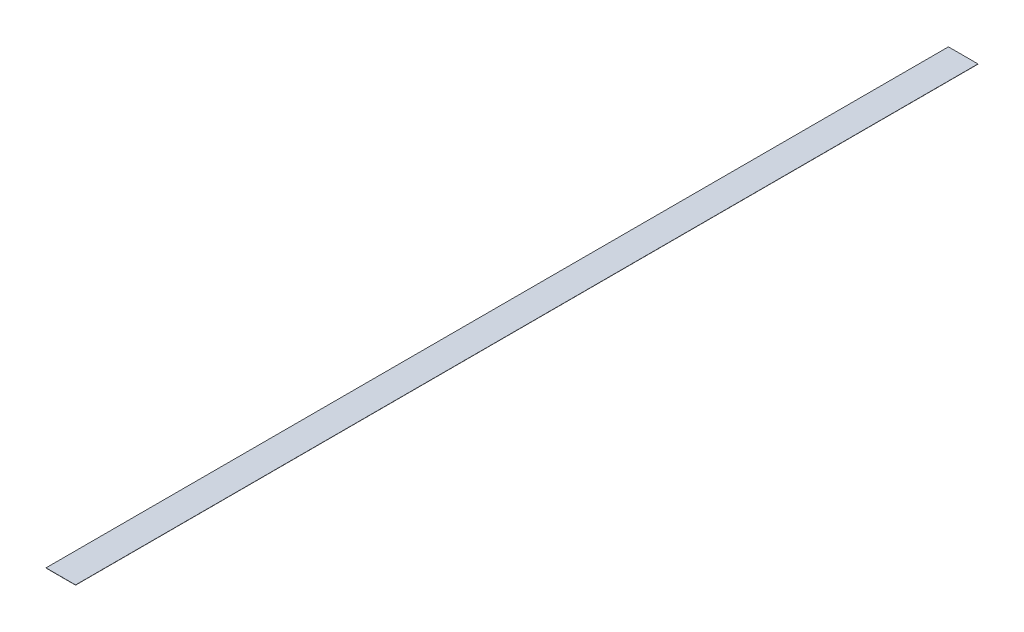
SolidWorks part; units mm, degrees
material "Kapton Film"
ref_plane "Front Plane" through (0, 0, 0) normal (0, 0, 1) x (1, 0, 0)
ref_plane "Top Plane" through (0, 0, 0) normal (0, 1, 0) x (1, 0, 0)
ref_plane "Right Plane" through (0, 0, 0) normal (1, 0, 0) x (0, 0, -1)
sketch "Sketch1" plane through (0, 0, 0) normal (0, 1, 0) x (1, 0, 0)
  line L5 (0, 0) -> (15, 0)
  line L6 (0, 0) -> (0, -457.6)
  line L7 (0, -457.6) -> (15, -457.6)
  line L8 (15, 0) -> (15, -457.6)
  dimension "D1" = 457.6
  dimension "D2" = 15
extrude "Boss-Extrude1" add sketch "Sketch1" along normal blind 0.1 contours L6 L7 L8 L5
sketch "Sketch2" plane through (0, 0.1, 0) normal (0, 1, 0) x (1, 0, 0)
  line L0 (0, -437.6) -> (15, -434.137) construction
  line L1 (0, 0) -> (0, -457.6) construction
  line L2 (15, 0) -> (15, -457.6) construction
  line L3 (5.0641, -436.4309) -> (5.0641, -407.8309) construction
  circle A0 centre (5.0641, -436.4309) radius 1
  circle A1 centre (9.9359, -435.3061) radius 1
  circle A2 centre (5.0641, -407.8309) radius 1
  circle A3 centre (9.9359, -406.7061) radius 1
  circle A4 centre (5.0641, -379.2309) radius 1
  circle A5 centre (9.9359, -378.1061) radius 1
  circle A6 centre (5.0641, -350.6309) radius 1
  circle A7 centre (9.9359, -349.5061) radius 1
  circle A8 centre (5.0641, -322.0309) radius 1
  circle A9 centre (9.9359, -320.9061) radius 1
  circle A10 centre (5.0641, -293.4309) radius 1
  circle A11 centre (9.9359, -292.3061) radius 1
  circle A12 centre (5.0641, -264.8309) radius 1
  circle A13 centre (9.9359, -263.7061) radius 1
  circle A14 centre (5.0641, -236.2309) radius 1
  circle A15 centre (9.9359, -235.1061) radius 1
  circle A16 centre (5.0641, -207.6309) radius 1
  circle A17 centre (9.9359, -206.5061) radius 1
  circle A18 centre (5.0641, -179.0309) radius 1
  circle A19 centre (9.9359, -177.9061) radius 1
  circle A20 centre (5.0641, -150.4309) radius 1
  circle A21 centre (9.9359, -149.3061) radius 1
  circle A22 centre (5.0641, -121.8309) radius 1
  circle A23 centre (9.9359, -120.7061) radius 1
  circle A24 centre (5.0641, -93.2309) radius 1
  circle A25 centre (9.9359, -92.1061) radius 1
  circle A26 centre (5.0641, -64.6309) radius 1
  circle A27 centre (9.9359, -63.5061) radius 1
  circle A28 centre (5.0641, -36.0309) radius 1
  circle A29 centre (9.9359, -34.9061) radius 1
  circle A30 centre (5.0641, -7.4309) radius 1
  circle A31 centre (9.9359, -6.3061) radius 1
  point P13 (7.5, -435.8685)
  dimension "D3" = 2
  dimension "D4" = 5
  dimension "D1" = 20
  dimension "D2" = 77
  dimension "D5" = 2.5
  dimension "D7" = 28.6
  dimension "D6" = 16
extrude "Cut-Extrude1" [suppressed] cut sketch "Sketch2" against normal through all
ref_plane "Plane1" through (7.5, 0, 0) normal (1, 0, 0) x (0, 0, -1)
sketch "Sketch3" [suppressed] plane through (0, 0.1, 0) normal (0, 1, 0) x (1, 0, 0)
  line L5 (15, 0) -> (15, -507) construction
  line L6 (0, 0) -> (15, 0)
  line L7 (0, 0) -> (0, -492)
  line L8 (0, -492) -> (15, -492)
  line L9 (15, 0) -> (15, -492)
  dimension "D1" = 15
extrude "Cut-Extrude2" [suppressed] cut sketch "Sketch3" against normal blind 10
